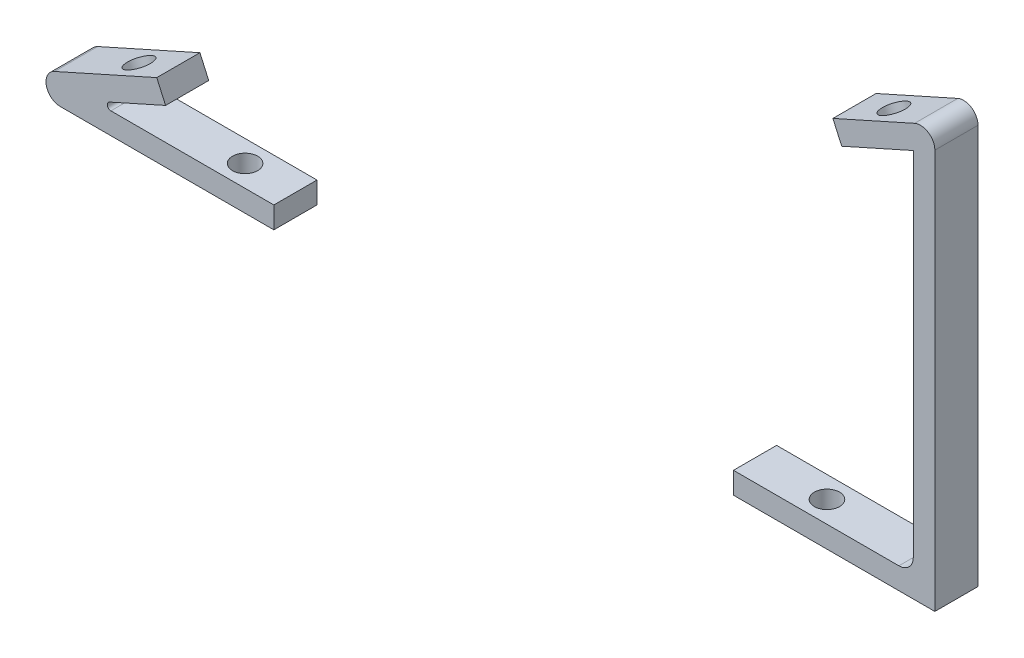
SolidWorks part; units mm, degrees
ref_plane "Front Plane" through (0, 0, 0) normal (0, 0, 1) x (1, 0, 0)
ref_plane "Top Plane" through (0, 0, 0) normal (0, 1, 0) x (1, 0, 0)
ref_plane "Right Plane" through (0, 0, 0) normal (1, 0, 0) x (0, 0, -1)
sketch "Sketch1" plane through (0, 0, 0) normal (0, 0, 1) x (1, 0, 0)
  line L0 (-25, 0) -> (0, 0)
  line L1 (88.9, 0) -> (88.9, 51)
  line L2 (-20.5294, 2.0018) -> (-15.0533, 4.4538)
  line L3 (88.9, 0) -> (63.9, 0)
  line L4 (63.9, 0) -> (63.9, -3)
  line L6 (88.9, 51) -> (84.4294, 48.9982)
  line L7 (-20.5294, 2.0018) -> (-25, 0)
  line L8 (63.9, -3) -> (91.9, -3)
  line L9 (91.9, -3) -> (91.9, 51)
  line L11 (0, 0) -> (0, -3)
  line L12 (0, -3) -> (-25, -3)
  line L14 (-15.0533, 4.4538) -> (-16.2792, 7.1918)
  line L16 (83.2034, 51.7363) -> (91.9, 55.6303)
  line L17 (91.9, 55.6303) -> (91.9, 51)
  line L18 (-16.2792, 7.1918) -> (-39.041, -3)
  line L19 (-39.041, -3) -> (-25, -3)
  line L20 (84.4294, 48.9982) -> (78.9533, 46.5462)
  line L21 (78.9533, 46.5462) -> (77.7273, 49.2843)
  line L22 (77.7273, 49.2843) -> (83.2034, 51.7363)
extrude "Boss-Extrude1" add sketch "Sketch1" along normal blind 6
fillet "Fillet1" radius 2 1 edges at (-39.041, -3, 3)
fillet "Fillet2" radius 2 1 edges at (91.9, 55.6303, 3)
fillet "Fillet3" radius 2 1 edges at (88.9, 0, 3)
fillet "Fillet4" radius 0.5 1 edges at (-25, 0, 3)
sketch "Sketch2" plane through (-5.4012, 12.0626, 0) normal (-0.4087, 0.9127, 0) x (0.9127, 0.4087, 0)
  circle A0 centre (97.0812, -3) radius 1.75
  circle A1 centre (-17.9188, -3) radius 1.75
extrude "Cut-Extrude1" cut sketch "Sketch2" against normal blind 3
sketch "Sketch3" plane through (0, 0, 0) normal (0, 1, 0) x (1, 0, 0)
  circle A0 centre (73.9, -3) radius 1.75
  circle A1 centre (-7, -3) radius 1.75
extrude "Cut-Extrude2" cut sketch "Sketch3" against normal blind 3
